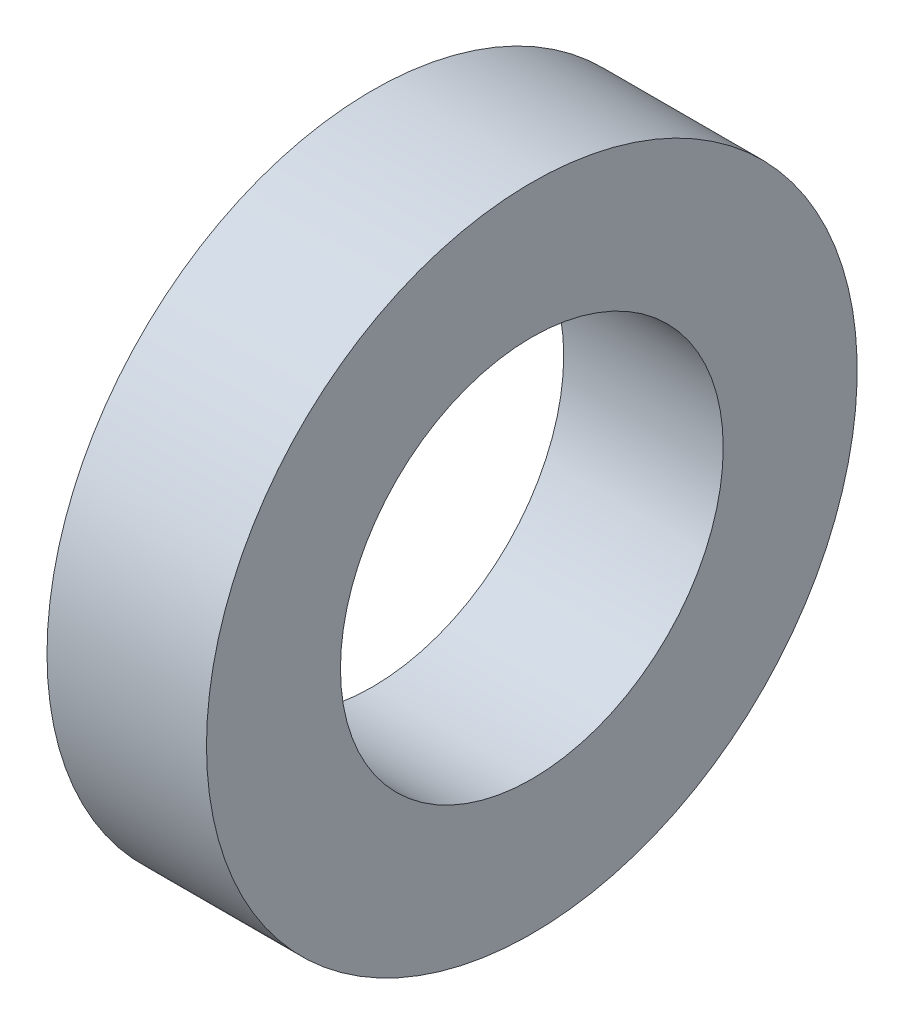
SolidWorks part; units mm, degrees
ref_plane "Plano frontal" through (0, 0, 0) normal (0, 0, 1) x (1, 0, 0)
ref_plane "Plano superior" through (0, 0, 0) normal (0, 1, 0) x (1, 0, 0)
ref_plane "Plano direito" through (0, 0, 0) normal (1, 0, 0) x (0, 0, -1)
ref_plane "Plano1" through (0, 0, 0) normal (0, 0, 1) x (1, 0, 0)
sketch "Esboço1" plane through (0, 0, 0) normal (0, 0, 1) x (1, 0, 0)
  line L0 (-7.9375, 16.1925) -> (-7.9375, 9.525)
  line L1 (-7.9375, 9.525) -> (0, 9.525)
  line L2 (0, 9.525) -> (0, 16.1925)
  line L3 (0, 16.1925) -> (-7.9375, 16.1925)
  line L4 (0, 0) -> (-7.9375, 0) construction
revolve "Revolução1" add sketch "Esboço1" angle 360 about L4
